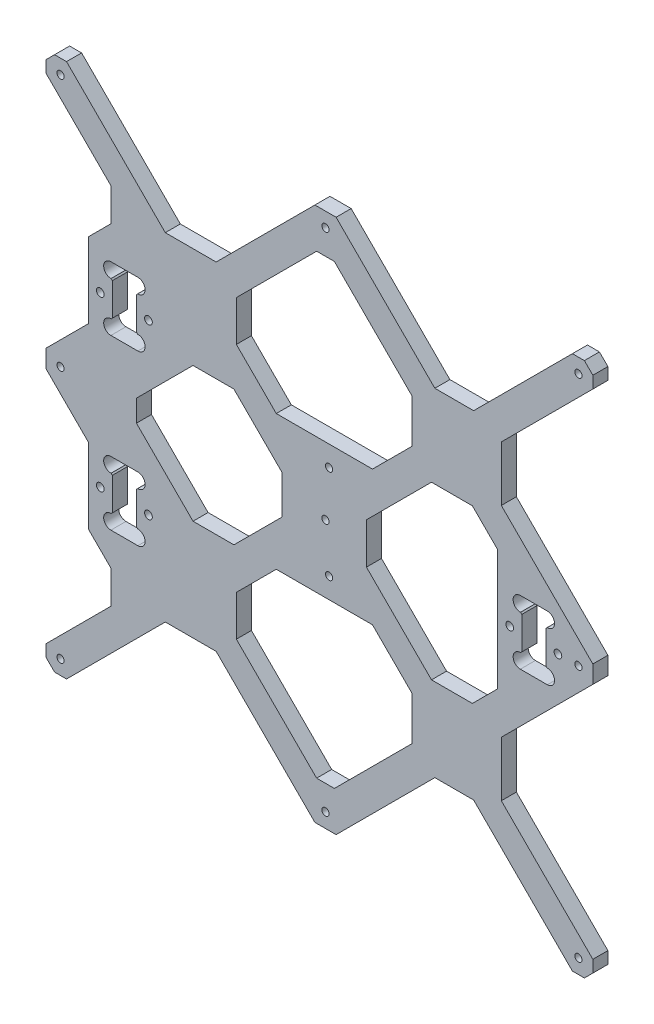
SolidWorks part; units mm, degrees
ref_plane "Front Plane" through (0, 0, 0) normal (0, 0, 1) x (1, 0, 0)
ref_plane "Top Plane" through (0, 0, 0) normal (0, 1, 0) x (1, 0, 0)
ref_plane "Right Plane" through (0, 0, 0) normal (1, 0, 0) x (0, 0, -1)
sketch "Model" plane through (0, 0, 0) normal (0, 0, 1) x (1, 0, 0)
  line L0 (-18, -7.977) -> (-38.023, -28)
  line L1 (-38.023, -28) -> (-55, -28)
  line L2 (-55, -28) -> (-78.5, -4.5)
  line L3 (-78.5, 4.5) -> (-55, 28)
  line L4 (-55, 28) -> (-38.023, 28)
  line L5 (-38.023, 28) -> (-18, 7.977)
  line L6 (71.5, 25.0147) -> (60.9853, 35.5294)
  line L7 (60.9853, 35.5294) -> (44.0147, 35.5294)
  line L8 (44.0147, 35.5294) -> (17, 8.5147)
  line L9 (17, -8.5147) -> (44.0147, -35.5294)
  line L10 (44.0147, -35.5294) -> (60.9853, -35.5294)
  line L11 (60.9853, -35.5294) -> (71.5, -25.0147)
  line L12 (4.4001, 111) -> (45.4001, 70)
  line L13 (45.4001, 70) -> (61.5147, 70)
  line L14 (61.5147, 70) -> (102.5147, 111)
  line L15 (102.5147, 111) -> (107.4852, 111)
  line L16 (107.4852, 111) -> (111, 107.4852)
  line L17 (111, 107.4852) -> (111, 102.5147)
  line L18 (111, 102.5147) -> (73, 64.5147)
  line L19 (73, 64.5147) -> (73, 41.667)
  line L20 (73, 41.667) -> (111, 3.667)
  line L21 (111, 3.667) -> (111, -3.667)
  line L22 (111, -3.667) -> (73, -41.667)
  line L23 (73, -41.667) -> (73, -64.5147)
  line L24 (73, -64.5147) -> (111, -102.5147)
  line L25 (111, -102.5147) -> (111, -107.4852)
  line L26 (111, -107.4852) -> (107.4852, -111)
  line L27 (107.4852, -111) -> (102.5147, -111)
  line L28 (102.5147, -111) -> (61.5147, -70)
  line L29 (61.5147, -70) -> (45.4001, -70)
  line L30 (45.4001, -70) -> (4.4001, -111)
  line L31 (4.4001, -111) -> (-4.4001, -111)
  line L32 (-4.4001, -111) -> (-45.4001, -70)
  line L33 (-45.4001, -70) -> (-66.5147, -70)
  line L34 (-66.5147, -70) -> (-107.5147, -111)
  line L35 (-107.5147, -111) -> (-112.4852, -111)
  line L36 (-112.4852, -111) -> (-116, -107.4852)
  line L37 (-116, -107.4852) -> (-116, -102.5147)
  line L38 (-116, -102.5147) -> (-89, -75.5147)
  line L39 (-89, -75.5147) -> (-89, -62)
  line L40 (-89, -62) -> (-98.5, -52.5)
  line L41 (-98.5, -52.5) -> (-98.5, -21.2391)
  line L42 (-98.5, -21.2391) -> (-116, -3.7391)
  line L43 (-116, 3.7391) -> (-98.5, 21.2391)
  line L44 (-98.5, 21.2391) -> (-98.5, 52.5)
  line L45 (-98.5, 52.5) -> (-89, 62)
  line L46 (-89, 62) -> (-89, 75.5147)
  line L47 (-89, 75.5147) -> (-116, 102.5147)
  line L48 (-116, 102.5147) -> (-116, 107.4852)
  line L49 (-116, 107.4852) -> (-112.4852, 111)
  line L50 (-112.4852, 111) -> (-107.5147, 111)
  line L51 (-107.5147, 111) -> (-66.5147, 70)
  line L52 (-66.5147, 70) -> (-45.4001, 70)
  line L53 (-45.4001, 70) -> (-4.4001, 111)
  line L54 (-4.4001, 111) -> (4.4001, 111)
  line L55 (-37, 61.4158) -> (-37, 44.5663)
  line L56 (-37, 44.5663) -> (-20.4337, 28)
  line L57 (-20.4337, 28) -> (19.5147, 28)
  line L58 (19.5147, 28) -> (36, 44.4853)
  line L59 (36, 44.4853) -> (36, 62.4296)
  line L60 (36, 62.4296) -> (3.6826, 94.747)
  line L61 (3.6826, 94.747) -> (-3.6826, 94.7332)
  line L62 (-3.6826, 94.7332) -> (-37, 61.4158)
  line L63 (-37, -61.4158) -> (-37, -44.5663)
  line L64 (-37, -44.5663) -> (-20.4337, -28)
  line L65 (-20.4337, -28) -> (19.5147, -28)
  line L66 (19.5147, -28) -> (36, -44.4853)
  line L67 (36, -44.4853) -> (36, -62.4296)
  line L68 (36, -62.4296) -> (3.6826, -94.747)
  line L69 (3.6826, -94.747) -> (-3.6826, -94.7332)
  line L70 (-3.6826, -94.7332) -> (-37, -61.4158)
  line L71 (-78.5, 41.75) -> (-78.5, 28.25)
  line L72 (91.5, 6.75) -> (91.5, -6.75)
  line L73 (-78.5, -28.25) -> (-78.5, -41.75)
  line L74 (-88.5, 41.75) -> (-88.5, 28.25)
  line L75 (81.5, 6.75) -> (81.5, -6.75)
  line L76 (-88.5, -28.25) -> (-88.5, -41.75)
  line L77 (-86.3208, 173.4107) -> (-86.3208, 162.8262)
  line L78 (-86.3208, 162.8262) -> (-86.0594, 160.7354)
  line L79 (-86.0594, 160.7354) -> (-85.5367, 159.2327)
  line L80 (-85.5367, 159.2327) -> (-84.818, 158.1873)
  line L81 (-84.818, 158.1873) -> (-83.8154, 156.9648)
  line L82 (-83.8154, 156.9648) -> (-82.1895, 156.4329)
  line L83 (-82.1895, 156.4329) -> (-80.3752, 156.0966)
  line L84 (-80.3752, 156.0966) -> (-78.023, 156.3579)
  line L85 (-78.023, 156.3579) -> (-75.9976, 157.4033)
  line L86 (-75.9976, 157.4033) -> (-74.8869, 159.2327)
  line L87 (-74.8869, 159.2327) -> (-74.4295, 161.7155)
  line L88 (-74.4295, 161.7155) -> (-74.4295, 164.1983)
  line L89 (-74.4295, 164.1983) -> (-74.4295, 173.4107)
  line L90 (-100.1068, 164.3289) -> (-99.9108, 164.3289)
  line L91 (-99.9108, 164.3289) -> (-98.9961, 163.8063)
  line L92 (-98.9961, 163.8063) -> (-97.9507, 162.4342)
  line L93 (-97.9507, 162.4342) -> (-93.5078, 156.0966)
  line L94 (-106.4444, 156.1619) -> (-106.4444, 173.4107)
  line L95 (-106.4444, 173.4107) -> (-99.3881, 173.4107)
  line L96 (-99.3881, 173.4107) -> (-97.232, 172.7574)
  line L97 (-97.232, 172.7574) -> (-96.1866, 171.7773)
  line L98 (-96.1866, 171.7773) -> (-95.4679, 170.4706)
  line L99 (-95.4679, 170.4706) -> (-95.1412, 168.7065)
  line L100 (-95.1412, 168.7065) -> (-95.4679, 167.0078)
  line L101 (-95.4679, 167.0078) -> (-96.3173, 165.5703)
  line L102 (-96.3173, 165.5703) -> (-97.4933, 164.8517)
  line L103 (-97.4933, 164.8517) -> (-98.6694, 164.525)
  line L104 (-98.6694, 164.525) -> (-100.1068, 164.3289)
  line L105 (-100.1068, 164.3289) -> (-101.8709, 164.3289)
  line L106 (-101.8709, 164.3289) -> (-106.4444, 164.3289)
  line L107 (-66.9103, 160.4442) -> (-65.7996, 158.4842)
  line L108 (-65.7996, 158.4842) -> (-63.3822, 156.8507)
  line L109 (-63.3822, 156.8507) -> (-61.0301, 156.1974)
  line L110 (-61.0301, 156.1974) -> (-57.5672, 156.7201)
  line L111 (-57.5672, 156.7201) -> (-55.9338, 158.0268)
  line L112 (-55.9338, 158.0268) -> (-54.7578, 160.1176)
  line L113 (-54.7578, 160.1176) -> (-54.7578, 161.359)
  line L114 (-54.7578, 161.359) -> (-55.0844, 162.4697)
  line L115 (-55.0844, 162.4697) -> (-56.2605, 163.7764)
  line L116 (-56.2605, 163.7764) -> (-57.4365, 164.2991)
  line L117 (-57.4365, 164.2991) -> (-63.2515, 166.0632)
  line L118 (-63.2515, 166.0632) -> (-64.9503, 167.1739)
  line L119 (-64.9503, 167.1739) -> (-65.9956, 168.4153)
  line L120 (-65.9956, 168.4153) -> (-66.1263, 169.5914)
  line L121 (-66.1263, 169.5914) -> (-65.865, 171.3554)
  line L122 (-65.865, 171.3554) -> (-64.6236, 172.6622)
  line L123 (-64.6236, 172.6622) -> (-62.5328, 173.4462)
  line L124 (-62.5328, 173.4462) -> (-59.9193, 173.5769)
  line L125 (-59.9193, 173.5769) -> (-57.1752, 172.8582)
  line L126 (-57.1752, 172.8582) -> (-56.0645, 171.8128)
  line L127 (-56.0645, 171.8128) -> (-55.6071, 170.5714)
  line L128 (-49.0046, 156.0312) -> (-42.0136, 173.5414)
  line L129 (-42.0136, 173.5414) -> (-40.9028, 173.5414)
  line L130 (-40.9028, 173.5414) -> (-34.0425, 156.0312)
  line L131 (-36.0657, 161.1951) -> (-46.9197, 161.1927)
  line L132 (-125, 156.1619) -> (-125, 173.4107)
  line L133 (-125, 173.4107) -> (-117.9437, 173.4107)
  line L134 (-117.9437, 173.4107) -> (-115.7875, 172.7574)
  line L135 (-115.7875, 172.7574) -> (-114.7422, 171.7773)
  line L136 (-114.7422, 171.7773) -> (-114.0235, 170.4706)
  line L137 (-114.0235, 170.4706) -> (-113.6968, 168.7065)
  line L138 (-113.6968, 168.7065) -> (-114.0235, 167.0078)
  line L139 (-114.0235, 167.0078) -> (-114.8728, 165.5703)
  line L140 (-114.8728, 165.5703) -> (-116.0489, 164.8517)
  line L141 (-116.0489, 164.8517) -> (-117.2249, 164.525)
  line L142 (-117.2249, 164.525) -> (-118.6624, 164.3289)
  line L143 (-118.6624, 164.3289) -> (-120.4265, 164.3289)
  line L144 (-120.4265, 164.3289) -> (-125, 164.3289)
  line L145 (71.5, 25.0147) -> (71.5, -25.0147)
  line L146 (17, 8.5147) -> (17, -8.5147)
  line L147 (-116, 3.7391) -> (-116, -3.7391)
  line L148 (-78.5, 4.5) -> (-78.5, -4.5)
  line L149 (-18, 7.977) -> (-18, -7.977)
  line L150 (-77.9, -42.25) -> (-78, -42.25)
  line L151 (92.1, -7.25) -> (92, -7.25)
  line L152 (-77.9, 27.75) -> (-78, 27.75)
  line L153 (-89.1, -42.25) -> (-89, -42.25)
  line L154 (80.9, -7.25) -> (81, -7.25)
  line L155 (-89.1, 27.75) -> (-89, 27.75)
  line L156 (-78, -42.25) -> (-78.5, -41.75)
  line L157 (92, -7.25) -> (91.5, -6.75)
  line L158 (-78, 27.75) -> (-78.5, 28.25)
  line L159 (-89, -42.25) -> (-88.5, -41.75)
  line L160 (81, -7.25) -> (81.5, -6.75)
  line L161 (-89, 27.75) -> (-88.5, 28.25)
  line L162 (-77.9, -27.75) -> (-78, -27.75)
  line L163 (92.1, 7.25) -> (92, 7.25)
  line L164 (-77.9, 42.25) -> (-78, 42.25)
  line L165 (-89.1, -27.75) -> (-89, -27.75)
  line L166 (80.9, 7.25) -> (81, 7.25)
  line L167 (-89.1, 42.25) -> (-89, 42.25)
  line L168 (-78.5, -28.25) -> (-78, -27.75)
  line L169 (91.5, 6.75) -> (92, 7.25)
  line L170 (-78.5, 41.75) -> (-78, 42.25)
  line L171 (-88.5, -28.25) -> (-89, -27.75)
  line L172 (81.5, 6.75) -> (81, 7.25)
  line L173 (-88.5, 41.75) -> (-89, 42.25)
  line L174 (-89.1, -21.75) -> (-77.9, -21.75)
  line L175 (80.9, 13.25) -> (92.1, 13.25)
  line L176 (-89.1, 48.25) -> (-77.9, 48.25)
  line L177 (-89.1, -48.25) -> (-77.9, -48.25)
  line L178 (80.9, -13.25) -> (92.1, -13.25)
  line L179 (-89.1, 21.75) -> (-77.9, 21.75)
  arc A0 (-77.9, 21.75) -> (-77.9, 27.75) centre (-77.9, 24.75) ccw
  arc A1 (92.1, -13.25) -> (92.1, -7.25) centre (92.1, -10.25) ccw
  arc A2 (-77.9, -48.25) -> (-77.9, -42.25) centre (-77.9, -45.25) ccw
  arc A3 (-89.1, -42.25) -> (-89.1, -48.25) centre (-89.1, -45.25) ccw
  arc A4 (-89.1, 27.75) -> (-89.1, 21.75) centre (-89.1, 24.75) ccw
  arc A5 (80.9, -7.25) -> (80.9, -13.25) centre (80.9, -10.25) ccw
  arc A6 (-77.9, -27.75) -> (-77.9, -21.75) centre (-77.9, -24.75) ccw
  arc A7 (-77.9, 42.25) -> (-77.9, 48.25) centre (-77.9, 45.25) ccw
  arc A8 (92.1, 7.25) -> (92.1, 13.25) centre (92.1, 10.25) ccw
  arc A9 (-89.1, -21.75) -> (-89.1, -27.75) centre (-89.1, -24.75) ccw
  arc A10 (80.9, 13.25) -> (80.9, 7.25) centre (80.9, 10.25) ccw
  arc A11 (-89.1, 48.25) -> (-89.1, 42.25) centre (-89.1, 45.25) ccw
  circle A12 centre (138.6, -180.1) radius 2.55
  circle A13 centre (138.6, -156.9) radius 2.55
  circle A14 centre (115.4, -156.9) radius 2.55
  circle A15 centre (115.4, -180.1) radius 2.55
  circle A16 centre (101.6, -180.1) radius 2.55
  circle A17 centre (78.4, -180.1) radius 2.55
  circle A18 centre (78.4, -156.9) radius 2.55
  circle A19 centre (101.6, -156.9) radius 2.55
  circle A20 centre (-68.4, -180.1) radius 2.55
  circle A21 centre (-68.4, -156.9) radius 2.55
  circle A22 centre (-91.6, -156.9) radius 2.55
  circle A23 centre (-91.6, -180.1) radius 2.55
  circle A24 centre (-105.4, -180.1) radius 2.55
  circle A25 centre (-105.4, -156.9) radius 2.55
  circle A26 centre (-128.6, -156.9) radius 2.55
  circle A27 centre (-128.6, -180.1) radius 2.55
  circle A28 centre (180, -145.2) radius 1.5
  circle A29 centre (-170, -145.2) radius 1.5
  circle A30 centre (160, 174.8) radius 1.5
  circle A31 centre (-150, -145.2) radius 1.5
  circle A32 centre (-137.1, -117.2) radius 1.5
  circle A33 centre (160, -145.2) radius 1.5
  circle A34 centre (-170, 174.8) radius 1.5
  circle A35 centre (170, -165.2) radius 1.5
  circle A36 centre (-133, -85.2) radius 1.5
  circle A37 centre (-176.3, -3.9) radius 1.5
  circle A38 centre (-160, -165.2) radius 1.5
  circle A39 centre (-175.1, -117.2) radius 1.5
  circle A40 centre (180, 174.8) radius 1.5
  circle A41 centre (-137.1, -23.2) radius 1.5
  circle A42 centre (-176.3, -85.2) radius 1.5
  circle A43 centre (-150, 174.8) radius 1.5
  circle A44 centre (-133, -10.3) radius 1.5
  circle A45 centre (-175.1, -23.2) radius 1.5
  circle A46 centre (-133.5, 84.3) radius 1.5
  circle A47 centre (-165, 62.8) radius 1.5
  circle A48 centre (-176.5, 84.3) radius 1.5
  circle A49 centre (-165, 105.8) radius 1.5
  circle A50 centre (0, -105) radius 1.5
  circle A51 centre (0, 105) radius 1.5
  circle A52 centre (105, -105) radius 1.5
  circle A53 centre (-110, 105) radius 1.5
  circle A54 centre (105, 105) radius 1.5
  circle A55 centre (-110, 0) radius 1.5
  circle A56 centre (0, 0) radius 1.5
  circle A57 centre (105, 0) radius 1.5
  circle A58 centre (76.5, 0) radius 1.6
  circle A59 centre (96.5, 0) radius 1.6
  circle A60 centre (-73.5, 35) radius 1.6
  circle A61 centre (-73.5, -35) radius 1.6
  circle A62 centre (-93.5, 35) radius 1.6
  circle A63 centre (-93.5, -35) radius 1.6
  circle A64 centre (-110, -105) radius 1.5
  circle A65 centre (1.5, -19.5) radius 1.5
  circle A66 centre (1.5, 19.5) radius 1.5
  circle A67 centre (-140, -178) radius 1.6
  circle A68 centre (151, -178) radius 1.6
  circle A69 centre (163, -178) radius 1.6
  circle A70 centre (-60, -172) radius 1.6
  circle A71 centre (-60, -181) radius 1.6
  circle A72 centre (50, -172) radius 1.6
  circle A73 centre (50, -181) radius 1.6
  circle A74 centre (153.4, 20) radius 2.1
  circle A75 centre (153.4, -97) radius 2.1
  circle A76 centre (-154, -178) radius 1.6
  circle A77 centre (-27, -172) radius 1.6
  circle A78 centre (-27, -181) radius 1.6
  spline S0 degree 2 poles (-175, 185) (-177.5, 182.5) (-180, 180) knots 1472.868668 1472.868668 1472.868668 1479.939736 1479.939736 1479.939736
  spline S1 degree 2 poles (185, 185) (5, 185) (-175, 185) knots 1112.868668 1112.868668 1112.868668 1472.868668 1472.868668 1472.868668
  spline S2 degree 2 poles (190, 180) (187.5, 182.5) (185, 185) knots 1105.7976 1105.7976 1105.7976 1112.868668 1112.868668 1112.868668
  spline S3 degree 2 poles (190, -180) (190, 0) (190, 180) knots 745.7976 745.7976 745.7976 1105.7976 1105.7976 1105.7976
  spline S4 degree 2 poles (185, -185) (187.5, -182.5) (190, -180) knots 738.726533 738.726533 738.726533 745.7976 745.7976 745.7976
  spline S5 degree 2 poles (165, -185) (175, -185) (185, -185) knots 718.726533 718.726533 718.726533 738.726533 738.726533 738.726533
  spline S6 degree 2 poles (161, -181) (163, -183) (165, -185) knots 710.241251 710.241251 710.241251 718.726533 718.726533 718.726533
  spline S7 degree 2 poles (153, -181) (157, -181) (161, -181) knots 704.241251 704.241251 704.241251 710.241251 710.241251 710.241251
  spline S8 degree 2 poles (149, -185) (151, -183) (153, -181) knots 698.584397 698.584397 698.584397 704.241251 704.241251 704.241251
  spline S9 degree 2 poles (-29, -185) (60, -185) (149, -185) knots 507.584397 507.584397 507.584397 698.584397 698.584397 698.584397
  spline S10 degree 2 poles (-34, -180) (-31.5, -182.5) (-29, -185) knots 501.927543 501.927543 501.927543 507.584397 507.584397 507.584397
  spline S11 degree 2 poles (-53, -180) (-43.5, -180) (-34, -180) knots 487.927543 487.927543 487.927543 501.927543 501.927543 501.927543
  spline S12 degree 2 poles (-58, -185) (-55.5, -182.5) (-53, -180) knots 482.270688 482.270688 482.270688 487.927543 487.927543 487.927543
  spline S13 degree 2 poles (-139, -185) (-98.5, -185) (-58, -185) knots 407.270688 407.270688 407.270688 482.270688 482.270688 482.270688
  spline S14 degree 2 poles (-143, -181) (-141, -183) (-139, -185) knots 401.613834 401.613834 401.613834 407.270688 407.270688 407.270688
  spline S15 degree 2 poles (-151, -181) (-147, -181) (-143, -181) knots 395.613834 395.613834 395.613834 401.613834 401.613834 401.613834
  spline S16 degree 2 poles (-155, -185) (-153, -183) (-151, -181) knots 387.128553 387.128553 387.128553 395.613834 395.613834 395.613834
  spline S17 degree 2 poles (-175, -185) (-165, -185) (-155, -185) knots 367.128553 367.128553 367.128553 387.128553 387.128553 387.128553
  spline S18 degree 2 poles (-180, -180) (-177.5, -182.5) (-175, -185) knots 360.191742 360.191742 360.191742 367.128553 367.128553 367.128553
  spline S19 degree 2 poles (-180, 180) (-180, 0) (-180, -180) knots 0 0 0 360.191742 360.191742 360.191742
  spline S20 degree 2 poles (-87, -153.5) (-80, -153.5) (-73, -153.5) knots 1110.421356 1110.421356 1110.421356 1117.046356 1117.046356 1117.046356
  spline S21 degree 2 poles (-92, -148.5) (-89.5, -151) (-87, -153.5) knots 1103.350288 1103.350288 1103.350288 1110.421356 1110.421356 1110.421356
  spline S22 degree 2 poles (-97, -148.5) (-94.5, -148.5) (-92, -148.5) knots 1098.350288 1098.350288 1098.350288 1103.350288 1103.350288 1103.350288
  spline S23 degree 2 poles (-107, -138.5) (-102, -143.5) (-97, -148.5) knots 1084.208153 1084.208153 1084.208153 1098.350288 1098.350288 1098.350288
  spline S24 degree 2 poles (-125, -138.5) (-116, -138.5) (-107, -138.5) knots 1066.208153 1066.208153 1066.208153 1084.208153 1084.208153 1084.208153
  spline S25 degree 2 poles (-130, -133.5) (-127.5, -136) (-125, -138.5) knots 1059.137085 1059.137085 1059.137085 1066.208153 1066.208153 1066.208153
  spline S26 degree 2 poles (-130, 140) (-130, 3.25) (-130, -133.5) knots 787.637085 787.637085 787.637085 1059.137085 1059.137085 1059.137085
  spline S27 degree 2 poles (-125, 145) (-127.5, 142.5) (-130, 140) knots 780.566017 780.566017 780.566017 787.637085 787.637085 787.637085
  spline S28 degree 2 poles (135, 145) (5, 145) (-125, 145) knots 520.566017 520.566017 520.566017 780.566017 780.566017 780.566017
  spline S29 degree 2 poles (140, 140) (137.5, 142.5) (135, 145) knots 513.494949 513.494949 513.494949 520.566017 520.566017 520.566017
  spline S30 degree 2 poles (140, -133.5) (140, 3.25) (140, 140) knots 241.994949 241.994949 241.994949 513.494949 513.494949 513.494949
  spline S31 degree 2 poles (135, -138.5) (137.5, -136) (140, -133.5) knots 234.923882 234.923882 234.923882 241.994949 241.994949 241.994949
  spline S32 degree 2 poles (117, -138.5) (126, -138.5) (135, -138.5) knots 216.923882 216.923882 216.923882 234.923882 234.923882 234.923882
  spline S33 degree 2 poles (107, -148.5) (112, -143.5) (117, -138.5) knots 202.781746 202.781746 202.781746 216.923882 216.923882 216.923882
  spline S34 degree 2 poles (102, -148.5) (104.5, -148.5) (107, -148.5) knots 197.781746 197.781746 197.781746 202.781746 202.781746 202.781746
  spline S35 degree 2 poles (97, -153.5) (99.5, -151) (102, -148.5) knots 190.710678 190.710678 190.710678 197.781746 197.781746 197.781746
  spline S36 degree 2 poles (83, -153.5) (90, -153.5) (97, -153.5) knots 176.710678 176.710678 176.710678 190.710678 190.710678 190.710678
  spline S37 degree 2 poles (78, -148.5) (80.5, -151) (83, -153.5) knots 169.63961 169.63961 169.63961 176.710678 176.710678 176.710678
  spline S38 degree 2 poles (30, -148.5) (54, -148.5) (78, -148.5) knots 121.63961 121.63961 121.63961 169.63961 169.63961 169.63961
  spline S39 degree 2 poles (10, -168.5) (20, -158.5) (30, -148.5) knots 93.355339 93.355339 93.355339 121.63961 121.63961 121.63961
  spline S40 degree 2 poles (0, -168.5) (5, -168.5) (10, -168.5) knots 83.355339 83.355339 83.355339 93.355339 93.355339 93.355339
  spline S41 degree 2 poles (-20, -148.5) (-10, -158.5) (0, -168.5) knots 55.071068 55.071068 55.071068 83.355339 83.355339 83.355339
  spline S42 degree 2 poles (-68, -148.5) (-44, -148.5) (-20, -148.5) knots 7.071068 7.071068 7.071068 55.071068 55.071068 55.071068
  spline S43 degree 2 poles (-73, -153.5) (-70.5, -151) (-68, -148.5) knots 0 0 0 7.071068 7.071068 7.071068
extrude "Boss-Extrude1" add sketch "Model" along normal blind 6.25 contours L43 L147 L42 L41 L40 L39 L38 L37 L36 L35 L34 L33 L32 L31 L30 L29 L28 L27 L26 L25 L24 L23 L22 L21 L20 L19 L18 L17 L16 L15 L14 L13 L12 L54 L53 L52 L51 L50 L49 L48 L47 L46 L45 L44 A66 A65 A64
